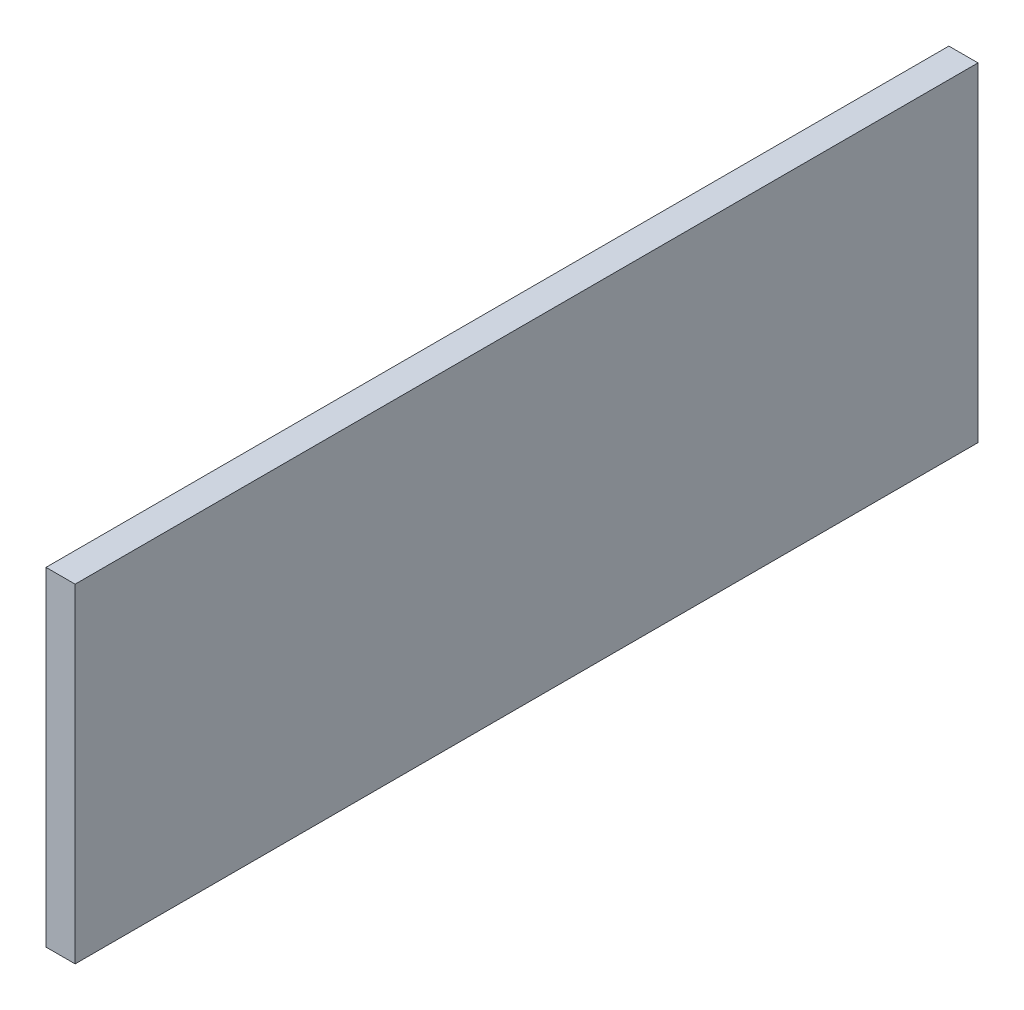
SolidWorks part; units mm, degrees
ref_plane "Front Plane" through (0, 0, 0) normal (0, 0, 1) x (1, 0, 0)
ref_plane "Top Plane" through (0, 0, 0) normal (0, 1, 0) x (1, 0, 0)
ref_plane "Right Plane" through (0, 0, 0) normal (1, 0, 0) x (0, 0, -1)
sketch "Sketch1" plane through (0, 0, 0) normal (1, 0, 0) x (0, 0, -1)
  line L1 (-51.9616, -56.7137) -> (41.0384, -56.7137)
  line L2 (-51.9616, -56.7137) -> (-51.9616, -22.8367)
  line L3 (-51.9616, -22.8367) -> (41.0384, -22.8367)
  line L4 (41.0384, -56.7137) -> (41.0384, -22.8367)
  point P0 (0, 0)
  point P6 (0, 0)
extrude "Boss-Extrude1" add sketch "Sketch1" along normal blind 3
